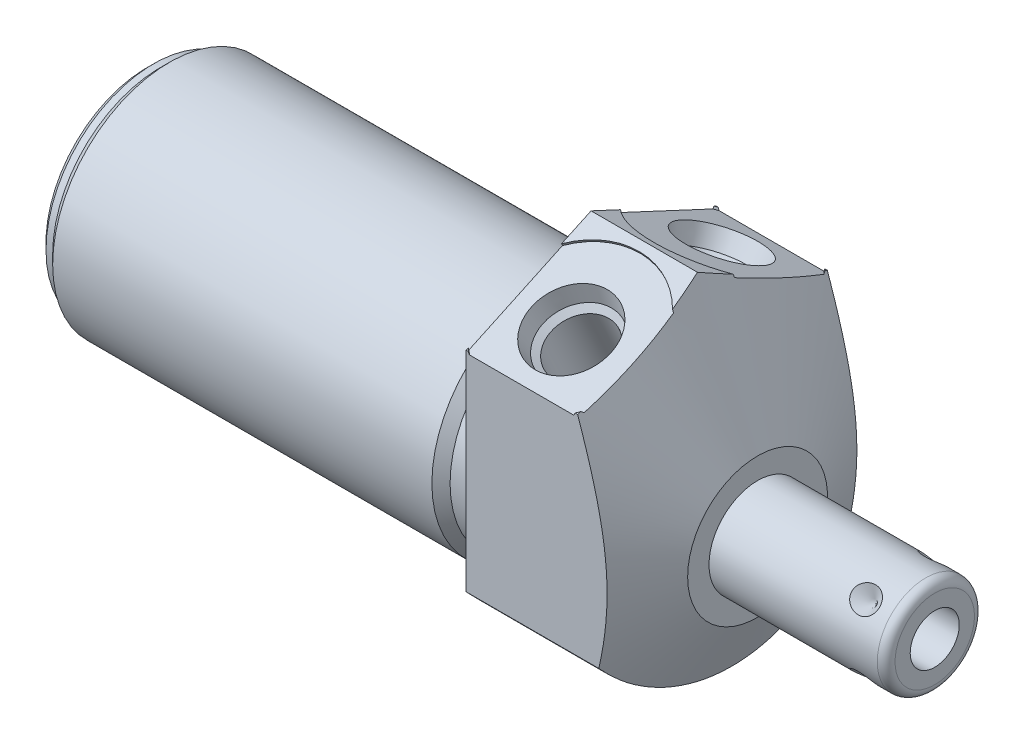
SolidWorks part; units mm, degrees
material "Alloy Steel"
ref_plane "Front Plane" through (0, 0, 0) normal (0, 0, 1) x (1, 0, 0)
ref_plane "Top Plane" through (0, 0, 0) normal (0, 1, 0) x (1, 0, 0)
ref_plane "Right Plane" through (0, 0, 0) normal (1, 0, 0) x (0, 0, -1)
ref_plane "Plane1" through (0, 0, 0) normal (1, 0, 0) x (0, 0, -1)
sketch "Sketch1" plane through (0, 0, 0) normal (1, 0, 0) x (0, 0, -1)
  circle A0 centre (0, 0) radius 19.05
  dimension "D1" = 38.1
extrude "Extrude1" add sketch "Sketch1" along normal blind 19.05 and the other way blind 50.8
ref_plane "Plane2" through (0, 0, 0) normal (1, 0, 0) x (0, 0, -1)
sketch "Sketch2" plane through (0, 0, 0) normal (1, 0, 0) x (0, 0, -1)
  line L0 (-14.6964, -4.7498) -> (14.6964, -4.7498) construction
  circle A0 centre (0, -4.7498) radius 13.3604
  circle A1 centre (0, 0) radius 19.05 construction
  circle A2 centre (0, 0) radius 19.05
  dimension "D1" = 26.7208
  dimension "D2" = 4.7498
extrude "Cut-Extrude1" cut sketch "Sketch2" against normal up to next
ref_plane "Plane4" through (0, 0, 0) normal (-1, 0, 0) x (0, 0, 1)
sketch "Sketch4" plane through (0, 0, 0) normal (-1, 0, 0) x (0, 0, 1)
  line L0 (14.2875, -12.6004) -> (14.2875, 11.3448)
  line L1 (14.2875, 11.3448) -> (0, 18.0071)
  line L2 (-14.2875, -12.6004) -> (-14.2875, 11.3448)
  line L3 (-14.2875, 11.3448) -> (0, 18.0071)
  line L4 (0, -20.9029) -> (0, 19.86) construction
  circle A0 centre (0, 0) radius 19.05 construction
  arc A1 (14.2875, -12.6004) -> (-14.2875, -12.6004) centre (0, 0) ccw
  dimension "D1" = 28.575
  dimension "D2" = 65
  dimension "D3" = 11.3448
extrude "Cut-Extrude3" cut sketch "Sketch4" against normal up to next
ref_plane "Plane6" through (0, 0, 0) normal (0, 0, 1) x (1, 0, 0)
sketch "Sketch6" plane through (0, 0, 0) normal (0, 0, 1) x (1, 0, 0)
  line L0 (12.1692, 18.0071) -> (19.05, 3.2512)
  line L1 (1.9872, -4.7498) -> (19.8625, -4.7498) construction
  line L2 (-50.8, -4.7498) -> (0, -4.7498) construction
  line L3 (19.05, 18.0071) -> (19.05, 11.3448) construction
  line L4 (19.05, 3.2512) -> (19.05, 18.0071)
  line L5 (19.05, 18.0071) -> (12.1692, 18.0071)
  line L6 (19.05, 18.0071) -> (0, 18.0071) construction
  dimension "D1" = 8.001
  dimension "D2" = 25
revolve "Cut-Revolve2" cut sketch "Sketch6" angle 360 about L1
ref_plane "Plane7" through (6.35, 13.7124, 8.6091) normal (1, 0, 0) x (0, 0.4226, -0.9063)
sketch "S2D0002" plane through (6.35, 13.7124, 8.6091) normal (1, 0, 0) x (0, 0.4226, -0.9063)
  line L0 (0, 0) -> (4.5466, 0)
  line L1 (4.5466, 0) -> (4.1066, -2.0701)
  line L2 (4.1066, -2.0701) -> (3.4544, -2.7223)
  line L3 (3.4544, -2.7223) -> (3.4544, -12.192)
  line L4 (3.4544, -12.192) -> (0, -12.192)
  line L5 (0, -12.192) -> (0, 0)
  line L6 (0, -12.8016) -> (0, 0.6096) construction
  dimension "D1" = 12.192
revolve "Cut-Revolve3" cut sketch "S2D0002" angle 360 about L6
ref_plane "Plane8" through (6.35, 13.7124, -8.6091) normal (1, 0, 0) x (0, -0.4226, -0.9063)
sketch "Sketch19" plane through (0, 14.791, 6.8971) normal (0, 0.9063, 0.4226) x (1, 0, 0)
  circle A0 centre (6.35, -2.0074) radius 8.6614
  dimension "D1" = 17.3228
extrude "Cut-Extrude4" cut sketch "Sketch19" against normal blind 0.254
sketch "Sketch8" plane through (6.35, 13.7124, -8.6091) normal (1, 0, 0) x (0, -0.4226, -0.9063)
  line L0 (0, 0) -> (4.5466, 0)
  line L1 (4.5466, 0) -> (4.1066, -2.0701)
  line L2 (4.1066, -2.0701) -> (3.4544, -2.7223)
  line L3 (3.4544, -2.7223) -> (3.4544, -12.192)
  line L4 (3.4544, -12.192) -> (0, -12.192)
  line L5 (0, -12.192) -> (0, 0)
  line L6 (0, -12.8016) -> (0, 0.6096) construction
  dimension "D1" = 12.192
revolve "Cut-Revolve4" cut sketch "Sketch8" angle 360 about L6
sketch "Sketch20" plane through (0, 14.791, -6.8971) normal (0, 0.9063, -0.4226) x (1, 0, 0)
  circle A0 centre (6.35, 2.0074) radius 8.6614
  dimension "D1" = 17.3228
extrude "Cut-Extrude5" cut sketch "Sketch20" against normal blind 0.254
ref_plane "Plane10" through (0, 0, 0) normal (0, 0, 1) x (1, 0, 0)
sketch "Sketch10" plane through (0, 0, 0) normal (0, 0, 1) x (1, 0, 0)
  line L0 (0, 8.6106) -> (0, 7.5692)
  line L1 (0, 7.5692) -> (-3.81, 7.5692)
  line L2 (-3.81, 7.5692) -> (-4.8514, 8.6106)
  line L3 (-5.094, -4.7498) -> (0.2426, -4.7498) construction
  line L4 (0, 8.6106) -> (-4.8514, 8.6106)
  line L5 (-50.8, -4.7498) -> (0, -4.7498) construction
  line L6 (0, 8.6106) -> (-50.8, 8.6106) construction
  line L7 (0, 11.3448) -> (0, -12.6004) construction
  dimension "D1" = 24.638
  dimension "D2" = 3.81
  dimension "D3" = 45
revolve "Cut-Revolve6" cut sketch "Sketch10" angle 360 about L3
ref_plane "Plane12" through (0, 0, 0) normal (0, 0, 1) x (1, 0, 0)
sketch "Sketch12" plane through (0, 0, 0) normal (0, 0, 1) x (1, 0, 0)
  line L0 (-50.8, 8.6106) -> (-50.8, 7.5692)
  line L1 (-50.8, 7.5692) -> (-49.276, 7.5692)
  line L2 (-49.276, 7.5692) -> (-48.2346, 8.6106)
  line L3 (-50.9283, -4.7498) -> (-48.1063, -4.7498) construction
  line L4 (-50.8, 8.6106) -> (-48.2346, 8.6106)
  line L5 (-50.8, -4.7498) -> (-4.8514, -4.7498) construction
  line L6 (-4.8514, 8.6106) -> (-50.8, 8.6106) construction
  line L7 (-50.8, 8.6106) -> (-50.8, -18.1102) construction
  dimension "D1" = 24.638
  dimension "D2" = 1.524
  dimension "D3" = 45
revolve "Cut-Revolve8" cut sketch "Sketch12" angle 360 about L3
chamfer "Chamfer1" distance 0.762 angle 45 1 edges at (-50.8, -4.7498, 12.319)
ref_plane "Plane13" through (0, 0, 0) normal (0, 0, 1) x (0, -1, 0)
sketch "Sketch13" plane through (0, 0, 0) normal (0, 0, 1) x (0, -1, 0)
  line L0 (4.7498, 19.05) -> (4.7498, 39.3192)
  line L1 (4.7498, 39.3192) -> (9.2901, 39.3192)
  line L2 (10.306, 38.3032) -> (10.306, 19.05)
  line L3 (10.306, 19.05) -> (4.7498, 19.05)
  line L4 (4.7498, 18.0365) -> (4.7498, 40.3327) construction
  line L5 (4.7498, -48.2346) -> (4.7498, -4.8514) construction
  line L6 (12.7508, 19.05) -> (-3.2512, 19.05) construction
  line L7 (-11.3448, 0) -> (12.6004, 0) construction
  arc A0 (10.306, 38.3032) -> (9.2901, 39.3192) centre (9.2901, 38.3032) ccw
  dimension "D2" = 1.016
  dimension "D1" = 39.3192
  dimension "D3" = 11.1125
revolve "Revolve1" add sketch "Sketch13" angle 360 about L4
ref_plane "Plane14" through (39.3192, -7.5565, 0) normal (0, 0, 1) x (0, -1, 0)
sketch "S2D0001" plane through (39.3192, -7.5565, 0) normal (0, 0, 1) x (0, -1, 0)
  line L0 (0, 0) -> (0, -10.16)
  line L1 (0, -10.16) -> (-2.8067, -11.8464)
  line L2 (0, 0) -> (-2.8067, 0)
  line L3 (-2.8067, 0) -> (-2.8067, -11.8464)
  line L4 (-2.8067, -12.4388) -> (-2.8067, 0.5923) construction
  line L5 (-2.8067, -1.016) -> (-2.8067, -20.2692) construction
  line L6 (1.7336, 0) -> (-7.347, 0) construction
  dimension "D1" = 5.6134
  dimension "D2" = 59
  dimension "D3" = 10.16
revolve "Cut-Revolve9" cut sketch "S2D0001" angle 360 about L4
ref_plane "Plane16" through (35.3568, -10.306, 0) normal (0, 0, 1) x (-1, 0, 0)
ref_plane "Plane17" through (0, -2.3749, -2.3749) normal (0, 0.7071, 0.7071) x (-1, 0, 0)
sketch "Sketch16" plane through (35.3568, -0.8209, -3.9289) normal (0, -0.7071, -0.7071) x (-1, 0, 0)
  line L0 (0, 0) -> (1.5875, 0)
  line L1 (1.5875, 0) -> (0, -1.5875)
  line L2 (0, 0) -> (0, -1.5875)
  line L3 (0, -3.4788) -> (0, 0.0794) construction
  line L4 (-3.9624, -1.016) -> (-3.9624, -10.0965) construction
  line L5 (16.3068, 0) -> (-2.9464, 0) construction
  dimension "D1" = 3.9624
  dimension "D2" = 3.175
  dimension "D3" = 45
revolve "Cut-Revolve10" cut sketch "Sketch16" angle 360 about L3
pattern_circular "CirPattern1" count 4 over 360 about axis through (18.0365, -4.7498, 0) along (-1, 0, 0) of "Cut-Revolve10"
